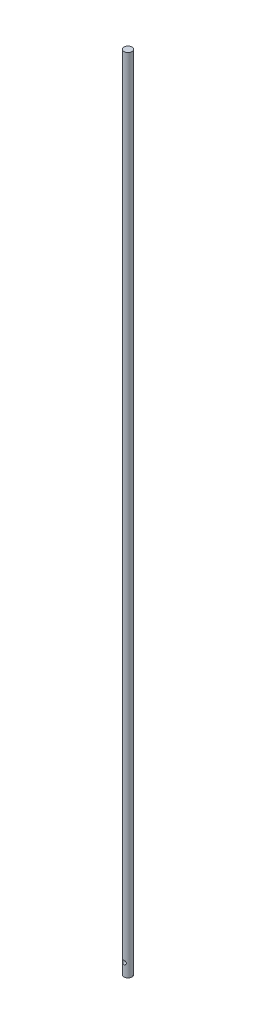
SolidWorks part; units mm, degrees
ref_plane "Front Plane" through (0, 0, 0) normal (0, 0, 1) x (1, 0, 0)
ref_plane "Top Plane" through (0, 0, 0) normal (0, 1, 0) x (1, 0, 0)
ref_plane "Right Plane" through (0, 0, 0) normal (1, 0, 0) x (0, 0, -1)
sketch "Sketch1" plane through (0, 0, 0) normal (0, 1, 0) x (1, 0, 0)
  circle A0 centre (0, 0) radius 3.175
  dimension "D1" = 6.35
extrude "Boss-Extrude1" add sketch "Sketch1" along normal blind 635
sketch "Sketch2" plane through (0, 6.35, 0) normal (0, 0, 1) x (-1, 0, 0)
  line L0 (3.175, 6.35) -> (-3.175, 6.35) construction
  circle A0 centre (0, -3.65) radius 1.5
  dimension "D2" = 3
  dimension "D1" = 10
extrude "Cut-Extrude1" cut sketch "Sketch2" against normal through all and the other way through all
